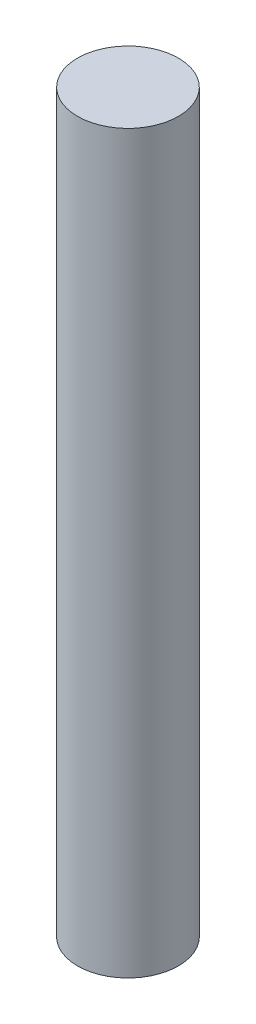
SolidWorks part; units mm, degrees
ref_plane "Front Plane" through (0, 0, 0) normal (0, 0, 1) x (1, 0, 0)
ref_plane "Top Plane" through (0, 0, 0) normal (0, 1, 0) x (1, 0, 0)
ref_plane "Right Plane" through (0, 0, 0) normal (1, 0, 0) x (0, 0, -1)
sketch "Sketch1" plane through (0, 0, 0) normal (0, 1, 0) x (1, 0, 0)
  circle A0 centre (-5.1193, 3.6567) radius 5
  dimension "D1" = 10
extrude "Boss-Extrude1" add sketch "Sketch1" along normal blind 72.9
